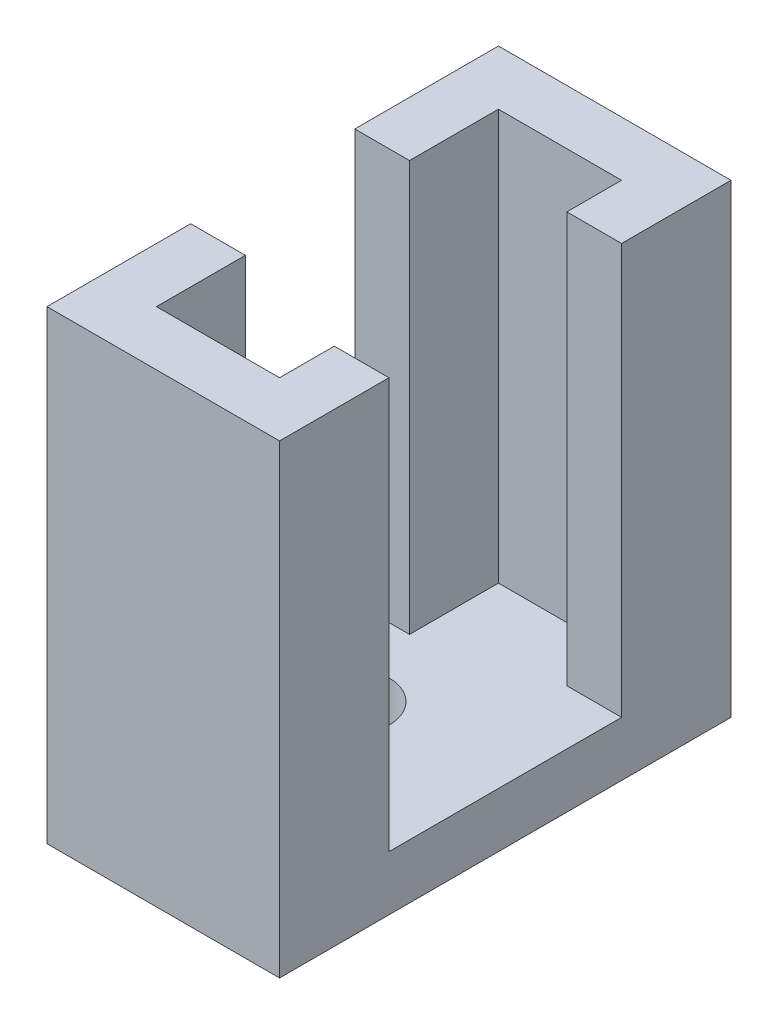
SolidWorks part; units mm, degrees
ref_plane "Front Plane" through (0, 0, 0) normal (0, 0, 1) x (1, 0, 0)
ref_plane "Top Plane" through (0, 0, 0) normal (0, 1, 0) x (1, 0, 0)
ref_plane "Right Plane" through (0, 0, 0) normal (1, 0, 0) x (0, 0, -1)
sketch "Sketch2" plane through (0, 0, 0) normal (0, 1, 0) x (1, 0, 0)
  line L0 (0, 0) -> (-4.5, 0)
  line L1 (-4.5, 0) -> (-4.5, -12.5)
  line L2 (-4.5, -12.5) -> (0, -12.5)
  line L3 (0, -12.5) -> (0, -10.5)
  line L4 (0, -10.5) -> (2, -10.5)
  line L5 (2, -10.5) -> (2, -14.5)
  line L6 (2, -14.5) -> (-6.5, -14.5)
  line L7 (-6.5, -14.5) -> (-6.5, 2)
  line L8 (-6.5, 2) -> (2, 2)
  line L9 (2, 2) -> (2, -2)
  line L10 (2, -2) -> (0, -2)
  line L11 (0, -2) -> (0, 0)
  dimension "D1" = 4.5
  dimension "D2" = 12.5
  dimension "D3" = 4.5
  dimension "D4" = 2
  dimension "D5" = 2
  dimension "D6" = 4
  dimension "D7" = 8.5
  dimension "D8" = 16.5
  dimension "D9" = 8.5
  dimension "D10" = 4
  dimension "D11" = 2
extrude "Boss-Extrude1" add sketch "Sketch2" along normal blind 15
sketch "Sketch3" plane through (0, 0, 0) normal (0, -1, 0) x (1, 0, 0)
  line L0 (-6.5, 14.5) -> (-3.5, 14.5) construction
  line L1 (-6.5, 14.5) -> (2, 14.5)
  line L2 (-6.5, 14.5) -> (-6.5, -2)
  line L3 (-6.5, -2) -> (2, -2)
  line L4 (2, 14.5) -> (2, -2)
  line L5 (-3.5, 14.5) -> (-3.5, 11.5) construction
  line L6 (-3.5, 11.5) -> (-3.5, 6.5) construction
  circle A0 centre (-3.5, 11.5) radius 1
  circle A1 centre (-3.5, 6.5) radius 1.5
  dimension "D3" = 2
  dimension "D5" = 3
  dimension "D1" = 3
  dimension "D2" = 3
  dimension "D4" = 5
extrude "Boss-Extrude2" add sketch "Sketch3" along normal blind 2
sketch "Sketch4" plane through (-4.5, 0, 0) normal (1, 0, 0) x (0, 0, -1)
  line L0 (-6.25, 0) -> (-6.25, 10) construction
  line L7 (-2, 0) -> (-10.5, 0) construction
  line L9 (-9.25, 20) -> (-3.25, 20)
  line L10 (-9.25, 20) -> (-9.25, 0)
  line L11 (-9.25, 0) -> (-3.25, 0)
  line L12 (-3.25, 20) -> (-3.25, 0)
  line L13 (-9.25, 20) -> (-3.25, 0) construction
  line L14 (-9.25, 0) -> (-3.25, 20) construction
  dimension "D1" = 10
  dimension "D2" = 20
  dimension "D3" = 6
extrude "Cut-Extrude1" cut sketch "Sketch4" against normal blind 2
